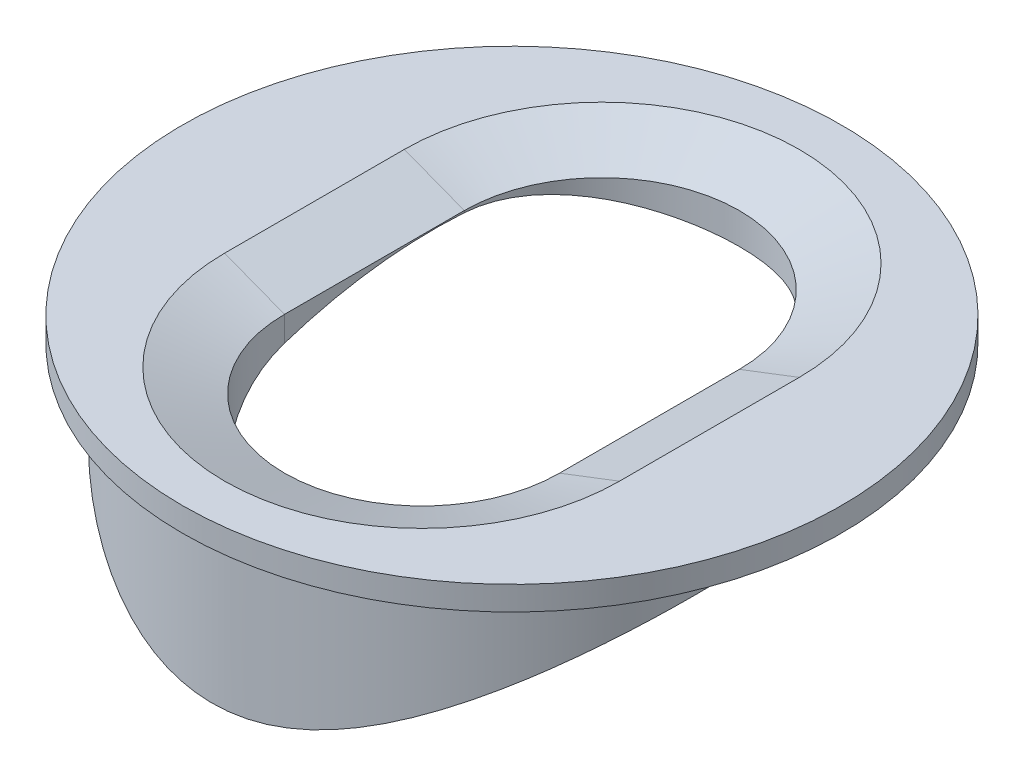
SolidWorks part; units mm, degrees
ref_plane "Front Plane" through (0, 0, 0) normal (0, 0, 1) x (1, 0, 0)
ref_plane "Top Plane" through (0, 0, 0) normal (0, 1, 0) x (1, 0, 0)
ref_plane "Right Plane" through (0, 0, 0) normal (1, 0, 0) x (0, 0, -1)
sketch "Sketch1" plane through (0, 0, 0) normal (0, 1, 0) x (1, 0, 0)
  circle A0 centre (0, 0) radius 5
extrude "Boss-Extrude1" add sketch "Sketch1" along normal blind 5
sketch "Sketch2" plane through (0, 5, 0) normal (0, 1, 0) x (1, 0, 0)
  circle A0 centre (0, 0) radius 5.5
extrude "Boss-Extrude2" add sketch "Sketch2" along normal blind 0.4
sketch "Sketch4" plane through (0, 5.4, 0) normal (0, 1, 0) x (1, 0, 0)
  line L0 (0, 1.5) -> (0, -1.5) construction
  line L1 (2.2953, 1.5) -> (2.2953, -1.5)
  line L2 (-2.2953, 1.5) -> (-2.2953, -1.5)
  arc A0 (2.2953, 1.5) -> (-2.2953, 1.5) centre (0, 1.5) ccw
  arc A1 (-2.2953, -1.5) -> (2.2953, -1.5) centre (0, -1.5) ccw
  point P3 (0, 0)
  dimension "D1" = 1.5
  dimension "D2" = 1.5
extrude "Cut-Extrude1" cut sketch "Sketch4" against normal through all
sketch "Sketch5" plane through (0, 0, 0) normal (1, 0, 0) x (0, 0, -1)
  circle A0 centre (1, -3) radius 8
extrude "Cut-Extrude2" cut sketch "Sketch5" against normal through all and the other way through all
chamfer "Chamfer4" distance 1 angle 21 4 edges at (0, 5.4, -3.7953) (-2.2953, 5.4, 0) (2.2953, 5.4, 0) (0, 5.4, 3.7953)
